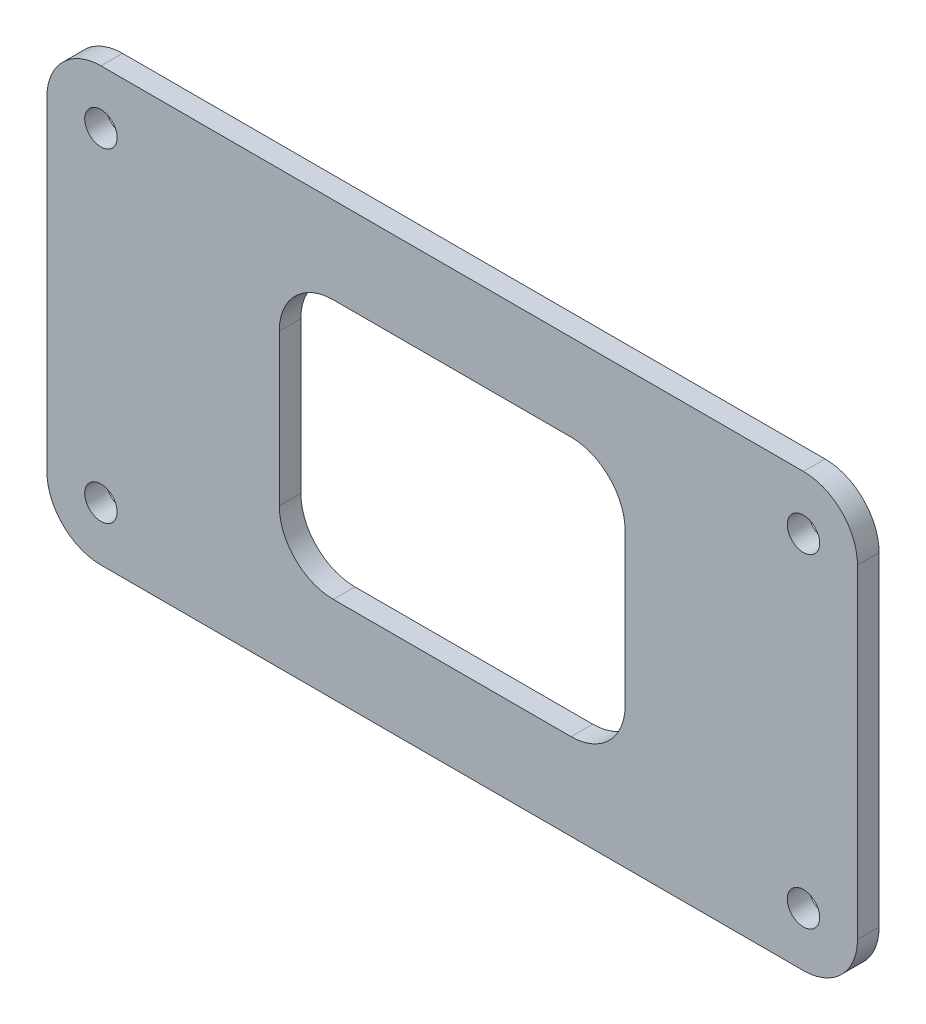
SolidWorks part; units mm, degrees
material "Hexcel AS4C (3000 Filaments)"
ref_plane "Front Plane" through (0, 0, 0) normal (0, 0, 1) x (1, 0, 0)
ref_plane "Top Plane" through (0, 0, 0) normal (0, 1, 0) x (1, 0, 0)
ref_plane "Right Plane" through (0, 0, 0) normal (1, 0, 0) x (0, 0, -1)
sketch "Sketch1" plane through (0, 0, 0) normal (0, 0, 1) x (1, 0, 0)
  line L0 (-32.5, -15) -> (-32.5, 15) construction
  line L1 (32.5, 20) -> (-32.5, 20)
  line L2 (37.5, 15) -> (37.5, -15)
  line L3 (32.5, -20) -> (-32.5, -20)
  line L4 (-37.5, 15) -> (-37.5, -15)
  line L5 (37.5, 20) -> (-37.5, -20) construction
  line L6 (37.5, -20) -> (-37.5, 20) construction
  line L7 (-11, 12) -> (11, 12)
  line L8 (-16, 7) -> (-16, -7)
  line L9 (-11, -12) -> (11, -12)
  line L10 (16, 7) -> (16, -7)
  line L11 (-16, 12) -> (16, -12) construction
  line L12 (-16, -12) -> (16, 12) construction
  line L13 (-32.5, 15) -> (32.5, 15) construction
  line L14 (32.5, 15) -> (32.5, -15) construction
  arc A0 (32.5, 20) -> (37.5, 15) centre (32.5, 15) cw
  arc A1 (-32.5, 20) -> (-37.5, 15) centre (-32.5, 15) ccw
  arc A2 (37.5, -15) -> (32.5, -20) centre (32.5, -15) cw
  arc A3 (-32.5, -20) -> (-37.5, -15) centre (-32.5, -15) cw
  arc A4 (-16, -7) -> (-11, -12) centre (-11, -7) ccw
  arc A5 (11, -12) -> (16, -7) centre (11, -7) ccw
  arc A6 (11, 12) -> (16, 7) centre (11, 7) cw
  arc A7 (-11, 12) -> (-16, 7) centre (-11, 7) ccw
  circle A8 centre (-32.5, -15) radius 1.5
  circle A9 centre (-32.5, 15) radius 1.5
  circle A10 centre (32.5, 15) radius 1.5
  circle A11 centre (32.5, -15) radius 1.5
  point P0 (0, 0)
  point P18 (0, 0)
  dimension "D1" = 5
  dimension "D2" = 5
  dimension "D7" = 5
  dimension "D9" = 3
  dimension "D3" = 75
  dimension "D4" = 40
  dimension "D5" = 32
  dimension "D6" = 24
  dimension "D8" = 30
extrude "Boss-Extrude1" add sketch "Sketch1" along normal blind 2
